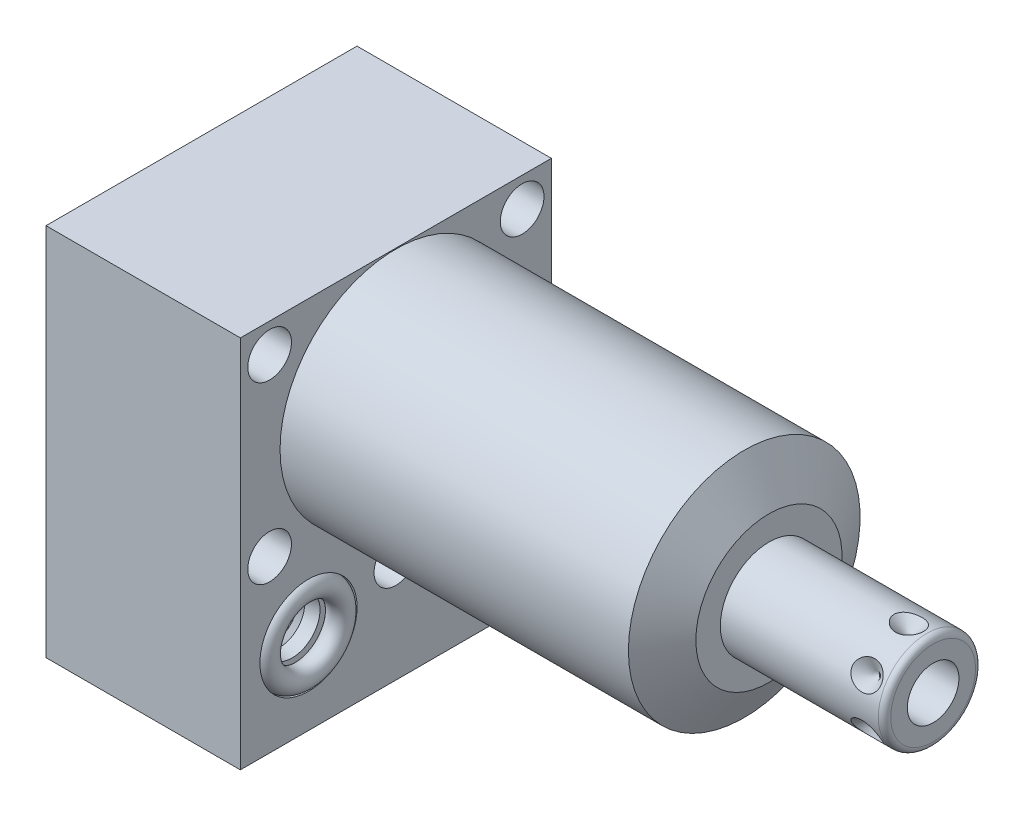
SolidWorks part; units mm, degrees
material "Alloy Steel"
ref_plane "Front Plane" through (0, 0, 0) normal (0, 0, 1) x (1, 0, 0)
ref_plane "Top Plane" through (0, 0, 0) normal (0, 1, 0) x (1, 0, 0)
ref_plane "Right Plane" through (0, 0, 0) normal (1, 0, 0) x (0, 0, -1)
ref_plane "Plane1" through (0, 0, 0) normal (1, 0, 0) x (0, 0, -1)
sketch "Sketch1" plane through (0, 0, 0) normal (1, 0, 0) x (0, 0, -1)
  line L0 (-25.4, 19.05) -> (-25.4, -42.0624)
  line L1 (-25.4, -42.0624) -> (25.4, -42.0624)
  line L2 (25.4, -42.0624) -> (25.4, 19.05)
  line L3 (25.4, 19.05) -> (-25.4, 19.05)
  line L4 (0, -47.0916) -> (0, 22.1996) construction
  dimension "D1" = 50.8
  dimension "D2" = 61.1124
  dimension "D3" = 19.05
extrude "Extrude1" add sketch "Sketch1" along normal blind 60.9346 and the other way blind 31.75
ref_plane "Plane2" through (0, 0, 0) normal (1, 0, 0) x (0, 0, -1)
sketch "Sketch2" plane through (0, 0, 0) normal (1, 0, 0) x (0, 0, -1)
  line L0 (-20.8153, 0) -> (20.8153, 0) construction
  line L6 (25.4, 19.05) -> (-25.4, 19.05)
  line L7 (-25.4, 19.05) -> (-25.4, -42.0624)
  line L8 (-25.4, -42.0624) -> (25.4, -42.0624)
  line L9 (25.4, -42.0624) -> (25.4, 19.05)
  line L10 (25.4, 19.05) -> (-25.4, 19.05)
  line L11 (-25.4, 19.05) -> (-25.4, -42.0624)
  line L12 (-25.4, -42.0624) -> (25.4, -42.0624)
  line L13 (25.4, -42.0624) -> (25.4, 19.05)
  circle A0 centre (0, 0) radius 18.923
  dimension "D1" = 37.846
  dimension "D2" = 0
extrude "Cut-Extrude1" cut sketch "Sketch2" along normal up to next
ref_plane "Plane3" through (0, 0, 0) normal (0, 0, 1) x (1, 0, 0)
sketch "Sketch3" plane through (0, 0, 0) normal (0, 0, 1) x (1, 0, 0)
  line L0 (56.9018, 18.923) -> (60.9346, 11.938)
  line L1 (56.7002, 0) -> (61.1362, 0) construction
  line L2 (60.9346, 18.923) -> (60.9346, 11.938)
  line L3 (60.9346, 18.923) -> (56.9018, 18.923)
  line L4 (60.9346, 18.923) -> (0, 18.923) construction
  line L5 (60.9346, -18.923) -> (60.9346, 18.923) construction
  dimension "D1" = 23.876
  dimension "D2" = 30
revolve "Cut-Revolve1" cut sketch "Sketch3" angle 360 about L1
ref_plane "Plane4" through (-29.083, -28.575, 14.2748) normal (0, 0, 1) x (0, 1, 0)
sketch "S2D0002" plane through (-29.083, -28.575, 14.2748) normal (0, 0, 1) x (0, 1, 0)
  line L0 (0, 0) -> (4.5466, 0)
  line L1 (4.5466, 0) -> (4.1066, -2.0701)
  line L2 (4.1066, -2.0701) -> (3.4544, -2.7223)
  line L3 (3.4544, -2.7223) -> (3.4544, -13.97)
  line L4 (3.4544, -13.97) -> (0, -13.97)
  line L5 (0, -13.97) -> (0, 0)
  line L6 (0, -14.6685) -> (0, 0.6985) construction
  dimension "D1" = 13.97
revolve "Cut-Revolve2" cut sketch "S2D0002" angle 360 about L6
ref_plane "Plane5" through (-29.083, -28.575, -14.2748) normal (0, 0, 1) x (0, 1, 0)
sketch "Sketch5" plane through (-29.083, -28.575, -14.2748) normal (0, 0, 1) x (0, 1, 0)
  line L0 (0, 0) -> (4.5466, 0)
  line L1 (4.5466, 0) -> (4.1066, -2.0701)
  line L2 (4.1066, -2.0701) -> (3.4544, -2.7223)
  line L3 (3.4544, -2.7223) -> (3.4544, -13.97)
  line L4 (3.4544, -13.97) -> (0, -13.97)
  line L5 (0, -13.97) -> (0, 0)
  line L6 (0, -14.6685) -> (0, 0.6985) construction
  dimension "D1" = 13.97
revolve "Cut-Revolve3" cut sketch "Sketch5" angle 360 about L6
ref_plane "Plane6" through (-2.667, -28.575, 14.2748) normal (0, 0, 1) x (0, -1, 0)
sketch "Sketch6" plane through (-2.667, -28.575, 14.2748) normal (0, 0, 1) x (0, -1, 0)
  line L0 (0, 0) -> (4.5466, 0)
  line L1 (4.5466, 0) -> (4.1066, -2.0701)
  line L2 (4.1066, -2.0701) -> (3.4544, -2.7223)
  line L3 (3.4544, -2.7223) -> (3.4544, -12.192)
  line L4 (3.4544, -12.192) -> (0, -12.192)
  line L5 (0, -12.192) -> (0, 0)
  line L6 (0, -12.8016) -> (0, 0.6096) construction
  dimension "D1" = 12.192
revolve "Cut-Revolve4" cut sketch "Sketch6" angle 360 about L6
ref_plane "Plane7" through (-2.667, -28.575, -14.2748) normal (0, 0, 1) x (0, -1, 0)
sketch "Sketch7" plane through (-2.667, -28.575, -14.2748) normal (0, 0, 1) x (0, -1, 0)
  line L0 (0, 0) -> (4.5466, 0)
  line L1 (4.5466, 0) -> (4.1066, -2.0701)
  line L2 (4.1066, -2.0701) -> (3.4544, -2.7223)
  line L3 (3.4544, -2.7223) -> (3.4544, -12.192)
  line L4 (3.4544, -12.192) -> (0, -12.192)
  line L5 (0, -12.192) -> (0, 0)
  line L6 (0, -12.8016) -> (0, 0.6096) construction
  dimension "D1" = 12.192
revolve "Cut-Revolve5" cut sketch "Sketch7" angle 360 about L6
ref_plane "Plane8" through (-15.875, -43.688, 14.2748) normal (0, 0, 1) x (-1, 0, 0)
sketch "Sketch18" plane through (-31.75, 0, 0) normal (-1, 0, 0) x (0, 0, 1)
  circle A0 centre (-14.2748, -28.575) radius 7.9375
  circle A1 centre (14.2748, -28.575) radius 7.9375
  dimension "D1" = 15.875
  dimension "D2" = 15.875
extrude "Cut-Extrude2" cut sketch "Sketch18" against normal blind 2.667
sketch "Sketch19" plane through (0, 0, 0) normal (1, 0, 0) x (0, 0, -1)
  circle A0 centre (-14.2748, -28.575) radius 7.9375
  circle A1 centre (14.2748, -28.575) radius 7.9375
  dimension "D1" = 15.875
  dimension "D2" = 15.875
extrude "Cut-Extrude3" cut sketch "Sketch19" against normal blind 2.667
sketch "Sketch8" plane through (-15.875, -43.688, 14.2748) normal (0, 0, 1) x (-1, 0, 0)
  line L0 (0, -1.8796) -> (6.1849, -1.8796)
  line L1 (6.1849, -1.8796) -> (5.6423, -4.4323)
  line L2 (5.6423, -4.4323) -> (4.9784, -5.0962)
  line L3 (4.9784, -5.0962) -> (4.9784, -20.9296)
  line L4 (4.9784, -20.9296) -> (0, -20.9296)
  line L5 (0, -20.9296) -> (0, -1.8796)
  line L6 (0, -26.67) -> (0, 1.27) construction
  line L7 (15.875, -1.6256) -> (-15.875, -1.6256) construction
  dimension "D1" = 19.05
  dimension "D2" = 0.254
revolve "Cut-Revolve6" cut sketch "Sketch8" angle 360 about L6
ref_plane "Plane9" through (-15.875, -43.688, -14.2748) normal (0, 0, 1) x (-1, 0, 0)
sketch "Sketch9" plane through (-15.875, -43.688, -14.2748) normal (0, 0, 1) x (-1, 0, 0)
  line L0 (0, -1.8796) -> (6.1849, -1.8796)
  line L1 (6.1849, -1.8796) -> (5.6423, -4.4323)
  line L2 (5.6423, -4.4323) -> (4.9784, -5.0962)
  line L3 (4.9784, -5.0962) -> (4.9784, -20.9296)
  line L4 (4.9784, -20.9296) -> (0, -20.9296)
  line L5 (0, -20.9296) -> (0, -1.8796)
  line L6 (0, -26.67) -> (0, 1.27) construction
  line L7 (15.875, -1.6256) -> (-15.875, -1.6256) construction
  dimension "D1" = 19.05
  dimension "D2" = 0.254
revolve "Cut-Revolve7" cut sketch "Sketch9" angle 360 about L6
ref_plane "Plane10" through (0, 0, 0) normal (0, 0, 1) x (1, 0, 0)
sketch "Sketch20" plane through (0, -42.0624, 0) normal (0, -1, 0) x (1, 0, 0)
  circle A0 centre (-15.875, 14.2748) radius 9.525
  circle A1 centre (-15.875, -14.2748) radius 9.525
  dimension "D1" = 19.05
extrude "Cut-Extrude4" cut sketch "Sketch20" against normal blind 0.254
sketch "Sketch10" plane through (0, 0, 0) normal (0, 0, 1) x (1, 0, 0)
  line L0 (60.9346, 0) -> (60.9346, 7.9375)
  line L1 (60.9346, 7.9375) -> (86.741, 7.9375)
  line L2 (87.757, 6.9215) -> (87.757, 0)
  line L3 (87.757, 0) -> (60.9346, 0)
  line L4 (59.5935, 0) -> (89.0981, 0) construction
  line L5 (60.9346, -11.938) -> (60.9346, 11.938) construction
  line L6 (-31.75, 19.05) -> (-31.75, -42.0624) construction
  arc A0 (87.757, 6.9215) -> (86.741, 7.9375) centre (86.741, 6.9215) ccw
  point P0 (60.9346, 0)
  dimension "D2" = 1.016
  dimension "D1" = 15.875
  dimension "D3" = 119.507
revolve "Revolve1" add sketch "Sketch10" angle 360 about L4
ref_plane "Plane11" through (87.757, -4.2164, 0) normal (0, 0, 1) x (0, -1, 0)
sketch "S2D0001" plane through (87.757, -4.2164, 0) normal (0, 0, 1) x (0, -1, 0)
  line L0 (0, 0) -> (0, -15.24)
  line L1 (0, -15.24) -> (-4.2164, -17.7735)
  line L2 (0, 0) -> (-4.2164, 0)
  line L3 (-4.2164, 0) -> (-4.2164, -17.7735)
  line L4 (-4.2164, -24.865) -> (-4.2164, 0.8887) construction
  line L5 (2.7051, 0) -> (-11.1379, 0) construction
  dimension "D1" = 8.4328
  dimension "D2" = 59
  dimension "D3" = 15.24
revolve "Cut-Revolve8" cut sketch "S2D0001" angle 360 about L4
ref_plane "Plane14" through (0, -28.575, -14.2748) normal (0, -1, 0) x (0, 0, -1)
sketch "Sketch14" plane through (0, -28.575, -14.2748) normal (0, -1, 0) x (0, 0, -1)
  line L0 (0, -2.8435) -> (0, 1.0401) construction
  line L1 (0, -2.667) -> (0, -4.7371) construction
  line L2 (7.9375, -2.667) -> (-7.9375, -2.667) construction
  circle A0 centre (6.1722, -0.9017) radius 1.7653
  dimension "D1" = 3.5306
  dimension "D2" = 12.3444
revolve "Revolve2" add sketch "Sketch14" angle 360 about L0
ref_plane "Plane15" through (0, -28.575, -14.2748) normal (0, -1, 0) x (0, 0, -1)
sketch "Sketch15" plane through (0, -28.575, -14.2748) normal (0, -1, 0) x (0, 0, -1)
  line L0 (0, -32.7901) -> (0, -28.9065) construction
  line L1 (0, -26.3607) -> (0, -19.4599) construction
  line L2 (-7.9375, -29.083) -> (7.9375, -29.083) construction
  circle A0 centre (6.1722, -30.8483) radius 1.7653
  dimension "D1" = 3.5306
  dimension "D2" = 12.3444
revolve "Revolve3" add sketch "Sketch15" angle 360 about L0
ref_plane "Plane16" through (83.7946, -7.9375, 0) normal (0, 0, 1) x (-1, 0, 0)
sketch "Sketch16" plane through (83.7946, -7.9375, 0) normal (0, 0, 1) x (-1, 0, 0)
  line L0 (0, 0) -> (2.413, 0)
  line L1 (2.413, 0) -> (0, -2.413)
  line L2 (0, 0) -> (0, -2.413)
  line L3 (0, -3.8054) -> (0, 0.1207) construction
  line L4 (22.86, 0) -> (-2.9464, 0) construction
  line L5 (-3.9624, -1.016) -> (-3.9624, -14.859) construction
  dimension "D1" = 3.9624
  dimension "D2" = 4.826
  dimension "D3" = 45
revolve "Cut-Revolve9" cut sketch "Sketch16" angle 360 about L3
pattern_circular "CirPattern1" count 6 over 360 about axis through (60.9356, 0, 0) along (-1, 0, 0) of "Cut-Revolve9"
hole_wizard "Hole1" positions "Sketch22" profile "Sketch21" legacy end condition up to next
sketch "Sketch22" plane through (0, 0, 0) normal (1, 0, 0) x (0, 0, -1)
  line L0 (0, 0) -> (-32.1908, 0) construction
  point P0 (-20.6248, 14.2748)
  point P1 (0, -25.0952)
  point P13 (-20.6248, -14.2748)
  point P14 (20.6248, 14.2748)
  point P15 (20.6248, -14.2748)
  dimension "D2" = 14.2748
  dimension "D3" = 25.0952
sketch "Sketch21" plane through (0, 14.2748, 20.6248) normal (0, 1, 0) x (0, 0, -1)
  line L0 (0, 0) -> (0, 31.75)
  line L1 (0, 31.75) -> (3.5687, 31.75)
  line L2 (3.5687, 31.75) -> (3.5687, 0)
  line L3 (3.5687, 0) -> (0, 0)
  line L4 (0, 110) -> (0, -10) construction
  dimension "Diameter" = 7.1374
  dimension "Depth" = 31.75
pattern_linear "LPattern1" count 2 spacing 28.5496 along (0, 0, 1) of "Revolve3", "Revolve2"
